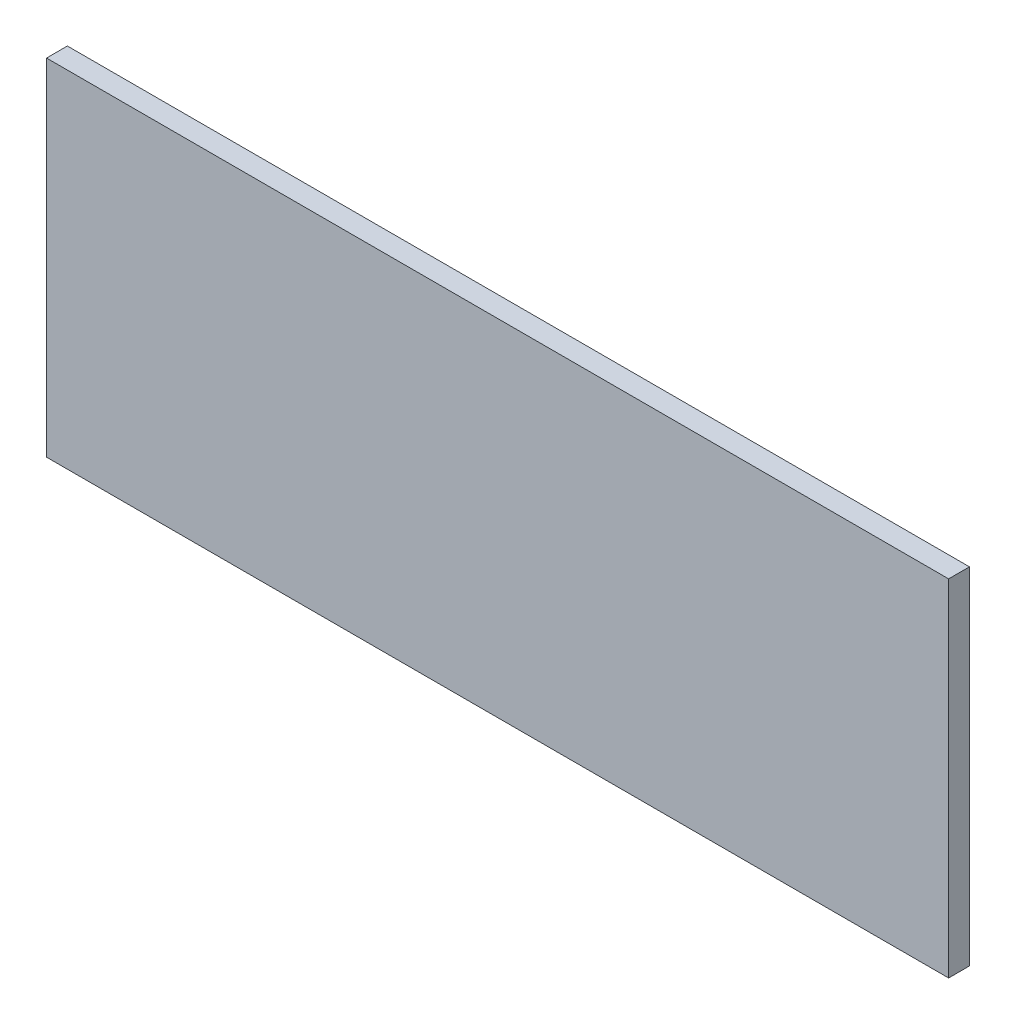
SolidWorks part; units mm, degrees
ref_plane "Front Plane" through (0, 0, 0) normal (0, 0, 1) x (1, 0, 0)
ref_plane "Top Plane" through (0, 0, 0) normal (0, 1, 0) x (1, 0, 0)
ref_plane "Right Plane" through (0, 0, 0) normal (1, 0, 0) x (0, 0, -1)
sketch "Sketch1" plane through (0, 0, 0) normal (0, 0, 1) x (1, 0, 0)
  line L1 (389.5, -149.25) -> (-389.5, -149.25)
  line L2 (389.5, -149.25) -> (389.5, 149.25)
  line L3 (389.5, 149.25) -> (-389.5, 149.25)
  line L4 (-389.5, -149.25) -> (-389.5, 149.25)
  line L5 (389.5, -149.25) -> (-389.5, 149.25) construction
  line L6 (389.5, 149.25) -> (-389.5, -149.25) construction
  point P0 (0, 0)
  dimension "D1" = 298.5
  dimension "D2" = 779
extrude "Boss-Extrude1" add sketch "Sketch1" along normal blind 18
equation "\"H_DSP\"=18"
equation "\"D1@Boss-Extrude1\"=\"H_DSP\""
